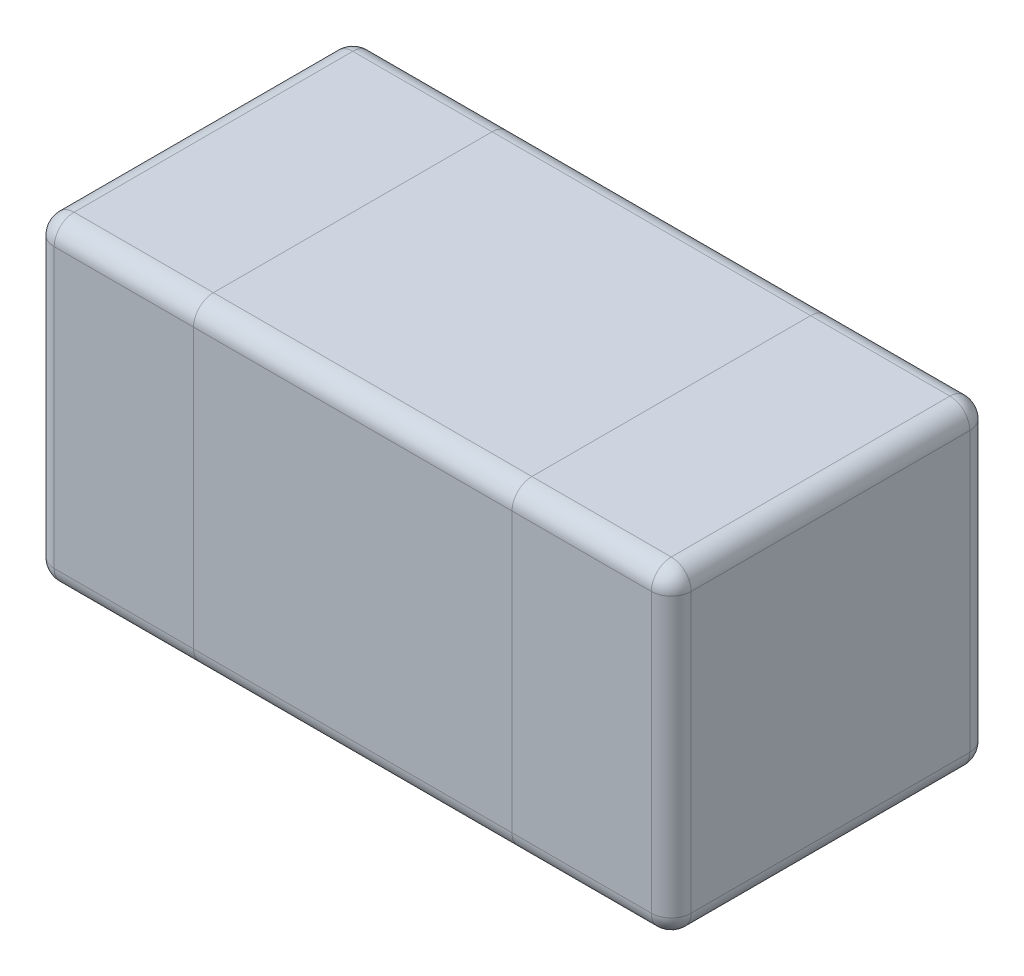
SolidWorks part; units mm, degrees
ref_plane "Front Plane" through (0, 0, 0) normal (0, 0, 1) x (1, 0, 0)
ref_plane "Top Plane" through (0, 0, 0) normal (0, 1, 0) x (1, 0, 0)
ref_plane "Right Plane" through (0, 0, 0) normal (1, 0, 0) x (0, 0, -1)
sketch "Sketch3" plane through (0, 0, 0) normal (0, 1, 0) x (1, 0, 0)
  line L1 (0, 0) -> (0.4, 0)
  line L2 (0, 0) -> (0, 0.8)
  line L3 (0, 0.8) -> (0.4, 0.8)
  line L4 (0.4, 0) -> (0.4, 0.8)
  line L5 (0.2, 0.8) -> (0.2, 0) construction
  line L6 (0, 0.4) -> (0.4, 0.4) construction
  line L7 (1.2, 0.8) -> (1.6, 0.8)
  line L8 (1.2, 0.8) -> (1.2, 0)
  line L9 (1.2, 0) -> (1.6, 0)
  line L10 (1.6, 0.8) -> (1.6, 0)
  line L11 (1.4, 0) -> (1.4, 0.8) construction
  line L12 (1.2, 0.4) -> (1.6, 0.4) construction
  point P100 (0.2, 0.4)
  point P138 (1.4, 0.4)
  dimension "D1" = 1.6
  dimension "D2" = 0.8
  dimension "D3" = 0.8
  dimension "D4" = 0.4
  dimension "D5" = 0.4
extrude "Boss-Extrude2" add sketch "Sketch3" along normal blind 0.8
sketch "Sketch4" plane through (0, 0, 0) normal (0, -1, 0) x (-1, 0, 0)
  line L1 (-0.4, 0.8) -> (-1.2, 0.8)
  line L2 (-0.4, 0.8) -> (-0.4, 0)
  line L3 (-0.4, 0) -> (-1.2, 0)
  line L4 (-1.2, 0.8) -> (-1.2, 0)
  line L5 (-0.8, 0) -> (-0.8, 0.8) construction
  line L6 (-0.4, 0.4) -> (-1.2, 0.4) construction
  point P164 (-0.8, 0.4)
extrude "Boss-Extrude3" add sketch "Sketch4" against normal blind 0.8 separate body
fillet "Fillet1" radius 0.05 8 edges at (0, 0.4, -0.8) (0, 0.8, -0.4) (0, 0.4, 0) (0, 0, -0.4) (0.2, 0.8, -0.8) (0.2, 0, -0.8) (0.2, 0, 0) (0.2, 0.8, 0)
fillet "Fillet2" radius 0.05 8 edges at (1.6, 0.4, 0) (1.6, 0.8, -0.4) (1.6, 0.4, -0.8) (1.6, 0, -0.4) (1.4, 0, 0) (1.4, 0, -0.8) (1.4, 0.8, 0) (1.4, 0.8, -0.8)
fillet "Fillet3" radius 0.05 4 edges at (0.8, 0, 0) (0.8, 0, -0.8) (0.8, 0.8, -0.8) (0.8, 0.8, 0)
sketch "Sketch5" plane through (0, 0.8, 0) normal (0, 1, 0) x (1, 0, 0)
  line L0 (0, 0.05) -> (0, 0.75) construction
  line L1 (0.4, 0.8) -> (1.2, 0.8) construction
  point P0 (0.8, 0.4)
  dimension "D1" = 0.8
  dimension "D2" = 0.4
